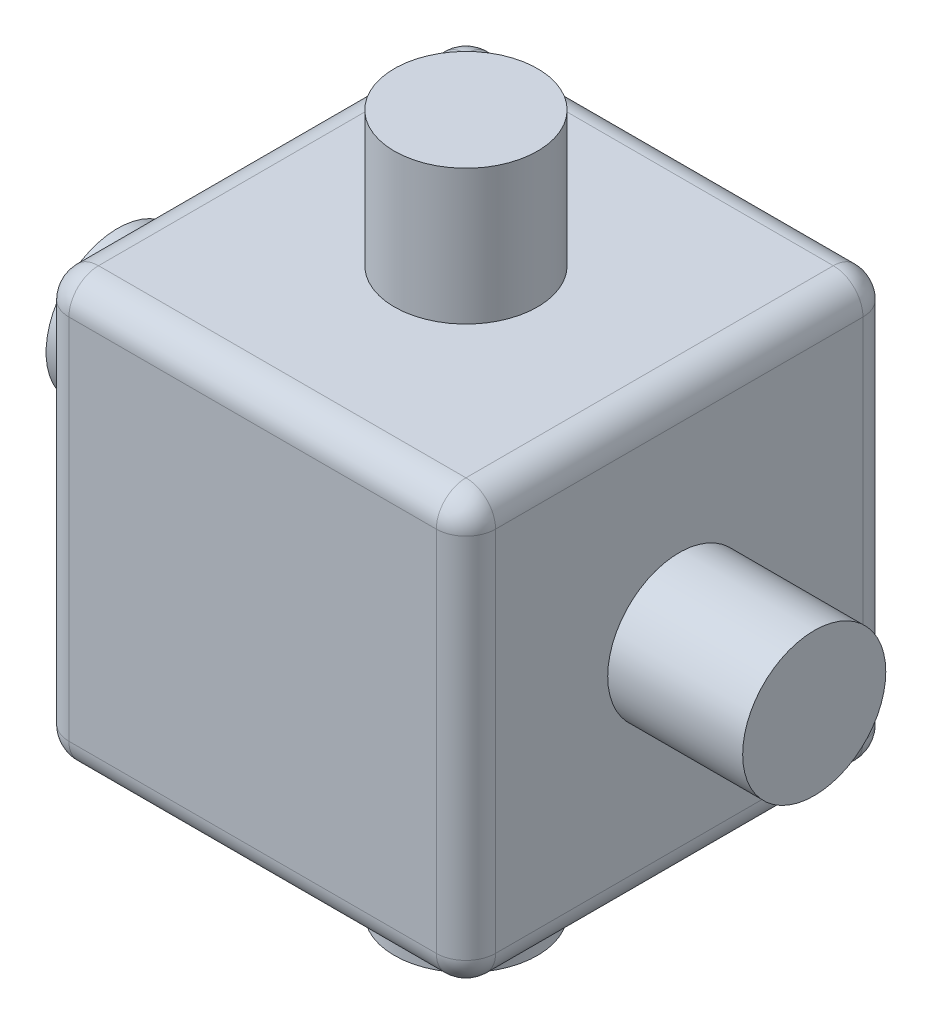
SolidWorks part; units mm, degrees
ref_plane "Front Plane" through (0, 0, 0) normal (0, 0, 1) x (1, 0, 0)
ref_plane "Top Plane" through (0, 0, 0) normal (0, 1, 0) x (1, 0, 0)
ref_plane "Right Plane" through (0, 0, 0) normal (1, 0, 0) x (0, 0, -1)
sketch "Sketch1" plane through (0, 0, 0) normal (0, 1, 0) x (1, 0, 0)
  line L1 (7.2, 7.2) -> (-7.2, 7.2)
  line L2 (-7.2, 7.2) -> (-7.2, -7.2)
  line L3 (-7.2, -7.2) -> (7.2, -7.2)
  line L4 (7.2, -7.2) -> (7.2, 7.2)
  circle A0 centre (0, 0) radius 7.2 construction
  dimension "D1" = 14.4
extrude "Boss-Extrude1" add sketch "Sketch1" along normal mid plane 14.4
sketch "Sketch2" plane through (0, 0, 0) normal (1, 0, 0) x (0, 0, -1)
  circle A0 centre (0, 0) radius 2.415
  dimension "D1" = 4.83
extrude "Boss-Extrude2" add sketch "Sketch2" along normal mid plane 23.51
sketch "Sketch3" plane through (0, 0, 0) normal (0, 1, 0) x (1, 0, 0)
  circle A0 centre (0, 0) radius 2.415
  dimension "D1" = 4.83
extrude "Boss-Extrude3" add sketch "Sketch3" along normal mid plane 23.51
fillet "Fillet2" radius 1 12 edges at (0, 7.2, 7.2) (-7.2, -7.2, 0) (-7.2, 0, 7.2) (0, -7.2, 7.2) (7.2, -7.2, 0) (7.2, 0, 7.2) (7.2, 7.2, 0) (0, -7.2, -7.2) (7.2, 0, -7.2) (-7.2, 7.2, 0) (-7.2, 0, -7.2) (0, 7.2, -7.2)
